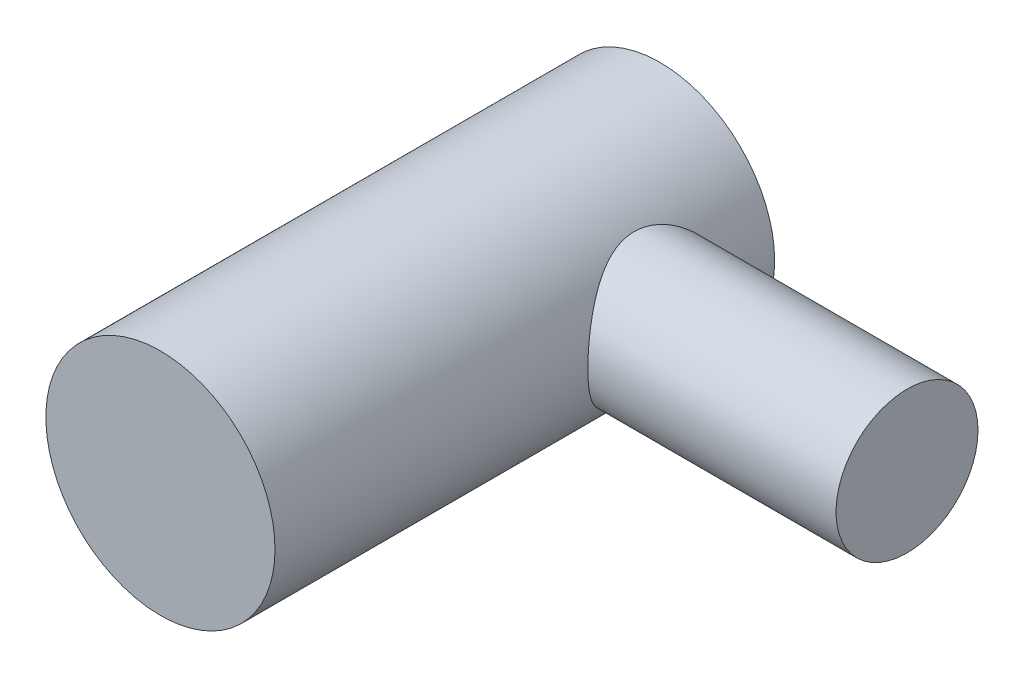
SolidWorks part; units mm, degrees
ref_plane "Front Plane" through (0, 0, 0) normal (0, 0, 1) x (1, 0, 0)
ref_plane "Top Plane" through (0, 0, 0) normal (0, 1, 0) x (1, 0, 0)
ref_plane "Right Plane" through (0, 0, 0) normal (1, 0, 0) x (0, 0, -1)
sketch "Sketch1" plane through (0, 0, 0) normal (0, 0, 1) x (1, 0, 0)
  circle A0 centre (0, 0) radius 18
  dimension "D1" = 36
extrude "Boss-Extrude1" add sketch "Sketch1" along normal blind 78.5
sketch "Sketch4" plane through (0, 0, 0) normal (1, 0, 0) x (0, 0, -1)
  line L0 (-78.5, 18) -> (-78.5, -18) construction
  circle A0 centre (-18.2, 0) radius 11.15
  dimension "D1" = 22.3
  dimension "D2" = 60.3
extrude "Boss-Extrude3" add sketch "Sketch4" along normal blind 57
